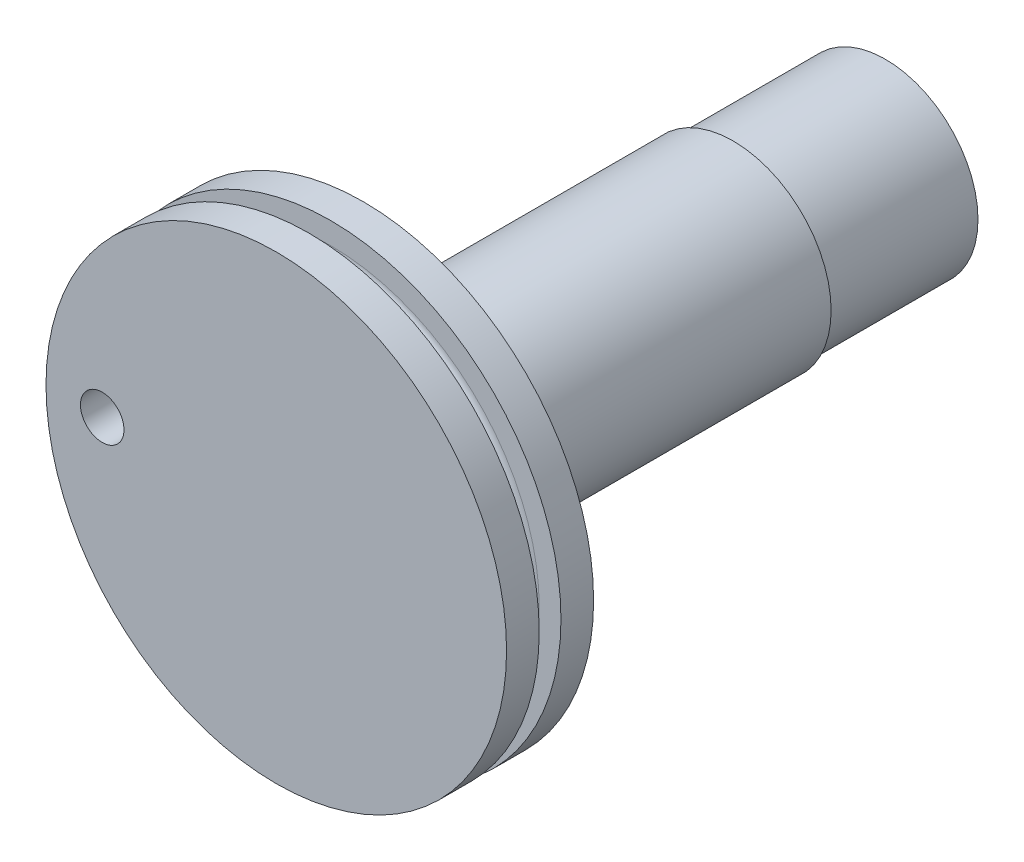
SolidWorks part; units mm, degrees
ref_plane "Front Plane" through (0, 0, 0) normal (0, 0, 1) x (1, 0, 0)
ref_plane "Top Plane" through (0, 0, 0) normal (0, 1, 0) x (1, 0, 0)
ref_plane "Right Plane" through (0, 0, 0) normal (1, 0, 0) x (0, 0, -1)
sketch "Sketch1" plane through (0, 0, 0) normal (0, 0, 1) x (1, 0, 0)
  line L1 (21, 78.5) -> (21, 75.75) construction
  circle A0 centre (21, 71.5) radius 4.25
  dimension "D1" = 8.5
extrude "Boss-Extrude1" add sketch "Sketch1" along normal blind 7
sketch "Sketch2" plane through (0, 0, 7) normal (0, 0, 1) x (1, 0, 0)
  circle A0 centre (21, 71.5) radius 4.5
  dimension "D1" = 9
extrude "Boss-Extrude2" add sketch "Sketch2" along normal blind 21
sketch "Sketch3" plane through (0, 0, 28) normal (0, 0, 1) x (1, 0, 0)
  circle A0 centre (21, 71.5) radius 10.5837
extrude "Boss-Extrude3" add sketch "Sketch3" against normal up to surface (4 mm away)
sketch "Sketch4" plane through (0, 0, 24) normal (0, 0, -1) x (-1, 0, 0)
  line L0 (-10.4163, 71.5) -> (-31.5837, 71.5) construction
  line L1 (-10.4163, 71.5) -> (-10.4163, 56.2487) construction
  circle A0 centre (-21, 71.5) radius 10.5837 construction
sketch "Sketch5" plane through (0, 0, 24) normal (0, 0, -1) x (-1, 0, 0)
  line L0 (-31.5837, 71.5) -> (-21, 71.5) construction
  circle A0 centre (-21, 71.5) radius 10.5837 construction
sketch3d "3DSketch1"
  line L0 (21, 71.5, 28) -> (21, 71.5, 0) construction
  line L1 (21, 71.5, 24) -> (21, 71.5, 28) construction
  line L2 (21, 71.5, 7) -> (21, 71.5, 0) construction
ref_plane "Plane1" through (0, 71.5, 0) normal (0, 1, 0) x (1, 0, 0)
sketch "Sketch6" plane through (0, 71.5, 0) normal (0, 1, 0) x (1, 0, 0)
  line L1 (31.5837, -24) -> (31.5837, -28) construction
  line L8 (31.5837, -24) -> (21, -24) construction
  line L9 (31.5837, -26.5) -> (31.5837, -25.5)
  line L10 (31.5837, -26.5) -> (30.5837, -26.5)
  line L11 (31.5837, -25.5) -> (30.5837, -25.5)
  arc A3 (30.5837, -25.5) -> (30.5837, -26.5) centre (30.5837, -26) ccw
  point P7 (31.5837, -26)
  dimension "D1" = 1
  dimension "D2" = 0.5
revolve "Cut-Revolve1" cut sketch "Sketch6" angle 360 about L0
sketch "Sketch8" plane through (0, 0, 24) normal (0, 0, -1) x (-1, 0, 0)
  line L0 (-21, 71.5) -> (-13, 71.5) construction
  circle A0 centre (-13, 71.5) radius 1
  dimension "D1" = 8
  dimension "D2" = 2
extrude "Cut-Extrude1" cut sketch "Sketch8" against normal up to surface (4 mm away) contours A0
